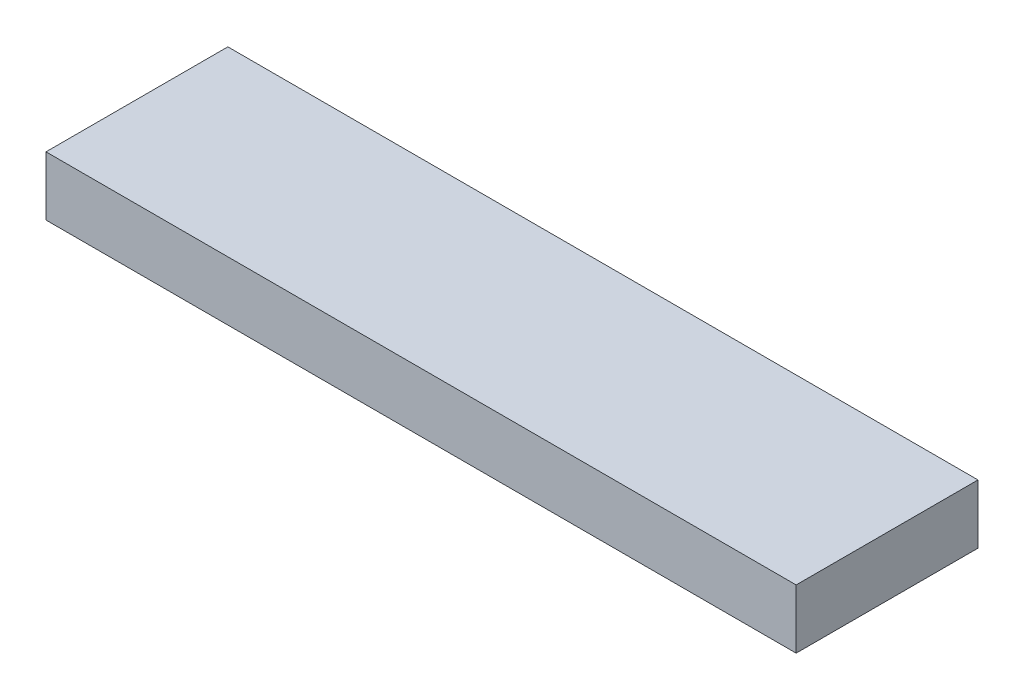
SolidWorks part; units mm, degrees
ref_plane "Front Plane" through (0, 0, 0) normal (0, 0, 1) x (1, 0, 0)
ref_plane "Top Plane" through (0, 0, 0) normal (0, 1, 0) x (1, 0, 0)
ref_plane "Right Plane" through (0, 0, 0) normal (1, 0, 0) x (0, 0, -1)
sketch "Sketch1" plane through (0, 0, 0) normal (0, 1, 0) x (1, 0, 0)
  line L1 (-20.955, 5.08) -> (20.955, 5.08)
  line L2 (-20.955, 5.08) -> (-20.955, -5.08)
  line L3 (-20.955, -5.08) -> (20.955, -5.08)
  line L4 (20.955, 5.08) -> (20.955, -5.08)
  line L5 (-20.955, 5.08) -> (20.955, -5.08) construction
  line L6 (-20.955, -5.08) -> (20.955, 5.08) construction
  point P0 (0, 0)
  dimension "D1" = 41.91
  dimension "D2" = 10.16
extrude "Boss-Extrude1" add sketch "Sketch1" along normal blind 3.302
sketch "Sketch2" plane through (0, 0, 0) normal (0, -1, 0) x (1, 0, 0)
  line L0 (0, 5.08) -> (0, -5.08) construction
  line L1 (-20.955, 5.08) -> (20.955, 5.08) construction
  line L2 (20.955, -5.08) -> (-20.955, -5.08) construction
  line L3 (-10.795, 5.08) -> (-10.795, -5.08) construction
  line L4 (-20.955, -5.08) -> (-20.955, 5.08) construction
  circle A0 centre (-13.462, 0) radius 1.174
  circle A1 centre (-8.128, 0) radius 1.174
  circle A2 centre (8.128, 0) radius 1.174
  circle A3 centre (13.462, 0) radius 1.174
  point P10 (-10.795, 0)
  dimension "D3" = 7.493
  dimension "D1" = 10.16
  dimension "D2" = 10.795
extrude "Boss-Extrude2" add sketch "Sketch2" along normal blind 0.635
